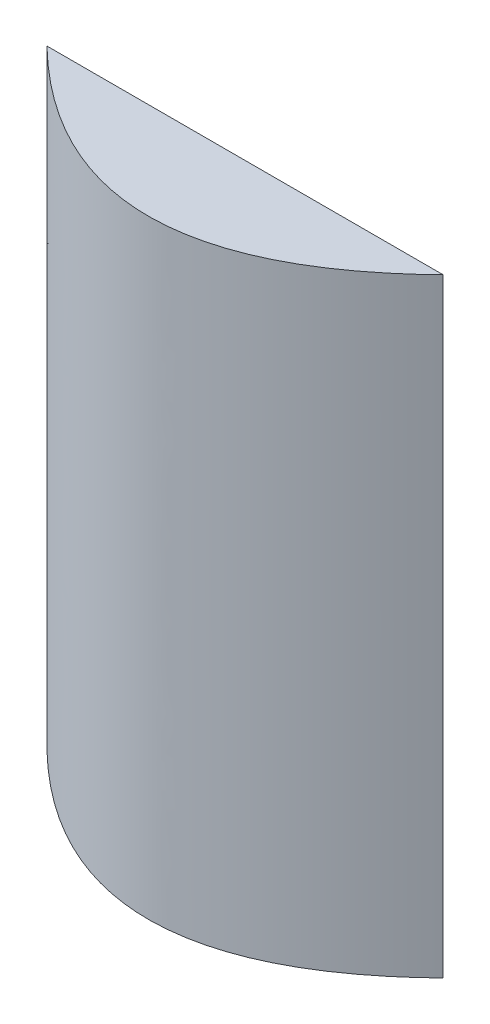
SolidWorks part; units mm, degrees
material "Custom Plastic (2)"
ref_plane "Front Plane" through (0, 0, 0) normal (0, 0, 1) x (1, 0, 0)
ref_plane "Top Plane" through (0, 0, 0) normal (0, 1, 0) x (1, 0, 0)
ref_plane "Right Plane" through (0, 0, 0) normal (1, 0, 0) x (0, 0, -1)
sketch "Sketch1" plane through (0, 0, 0) normal (0, 1, 0) x (1, 0, 0)
  line L0 (-200, 0) -> (200, 0)
  spline S0 degree 2 poles (-225.2396, 53.6645) (0, -453.6645) (225.2396, 53.6645) knots 0 0 0 1 1 1 construction
  spline S1 degree 2 poles (-200, 0) (0, -400) (200, 0) knots 0.056028 0.056028 0.056028 0.943972 0.943972 0.943972
extrude "Boss-Extrude1" add sketch "Sketch1" along normal blind 300
sketch "Sketch2" plane through (0, 300, 0) normal (0, 1, 0) x (1, 0, 0)
  line L0 (200, 0) -> (-200, 0) construction
  line L1 (-242.4448, 17.0673) -> (277.048, 17.0673)
  line L2 (-242.4448, 17.0673) -> (-242.4448, -152.4)
  line L3 (-242.4448, -152.4) -> (277.048, -152.4)
  line L4 (277.048, 17.0673) -> (277.048, -152.4)
  dimension "D1" = 152.4
extrude "Cut-Extrude1" cut sketch "Sketch2" against normal blind 350
